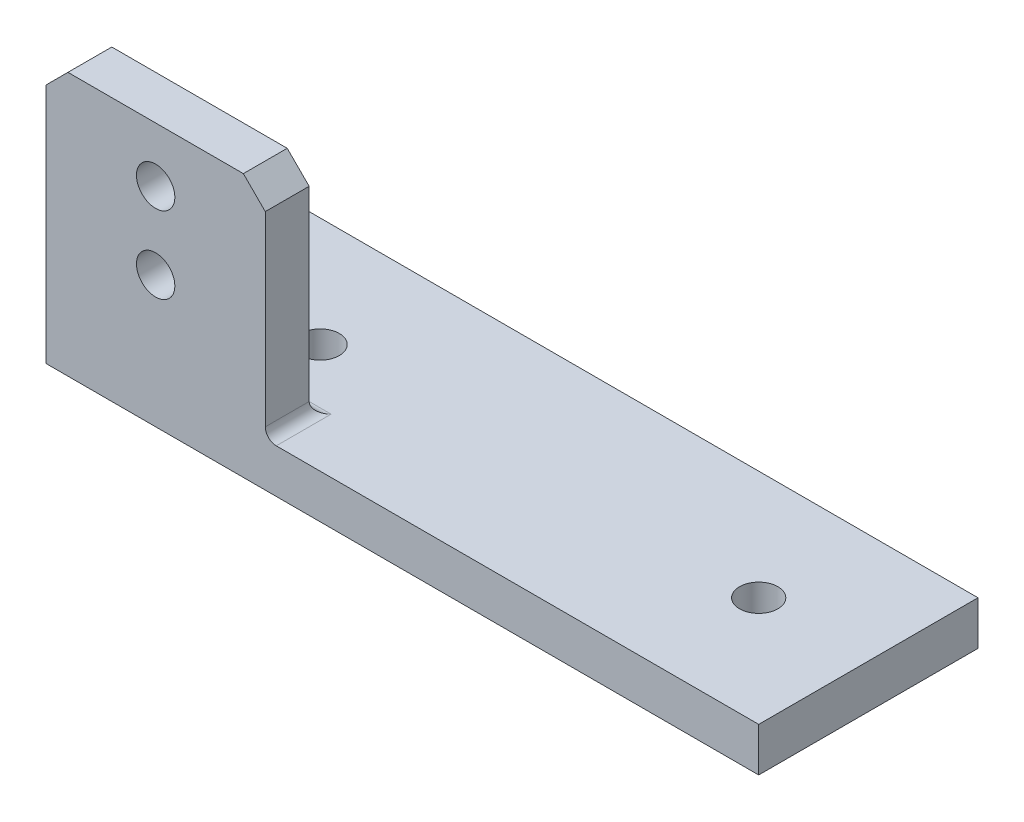
SolidWorks part; units mm, degrees
ref_plane "Piano frontale" through (0, 0, 0) normal (0, 0, 1) x (1, 0, 0)
ref_plane "Piano superiore" through (0, 0, 0) normal (0, 1, 0) x (1, 0, 0)
ref_plane "Piano destro" through (0, 0, 0) normal (1, 0, 0) x (0, 0, -1)
sketch "Schizzo1" plane through (0, 0, 0) normal (0, 0, 1) x (1, 0, 0)
  line L0 (0, 0) -> (65, 0)
  line L1 (65, 0) -> (65, 4)
  line L2 (65, 4) -> (0, 4)
  line L3 (0, 4) -> (0, 0)
  dimension "D1" = 4
  dimension "D2" = 65
extrude "Estrusione-Estrusione1" add sketch "Schizzo1" along normal blind 20
sketch "Schizzo2" plane through (0, 4, 0) normal (0, 1, 0) x (1, 0, 0)
  line L1 (0, -20) -> (20, -20)
  line L2 (0, -20) -> (0, -16)
  line L3 (0, -16) -> (20, -16)
  line L4 (20, -20) -> (20, -16)
  dimension "D1" = 4
  dimension "D2" = 20
extrude "Estrusione-Estrusione2" add sketch "Schizzo2" along normal blind 20
sketch "Schizzo6" plane through (0, 4, 0) normal (0, 1, 0) x (1, 0, 0)
  line L0 (65, -10) -> (0, -10) construction
  line L3 (65, -20) -> (65, 0) construction
  line L4 (0, -16) -> (0, 0) construction
  circle A0 centre (15, -10) radius 1.75
  circle A1 centre (55, -10) radius 1.75
  dimension "D1" = 3.5
  dimension "D2" = 10
  dimension "D3" = 40
extrude "Taglio-Estrusione1" cut sketch "Schizzo6" against normal up to next
sketch "Schizzo7" plane through (0, 0, 16) normal (0, 0, -1) x (-1, 0, 0)
  line L0 (-10, 24) -> (-10, 4) construction
  line L1 (-20, 24) -> (0, 24) construction
  line L2 (-20, 4) -> (0, 4) construction
  circle A0 centre (-10, 19) radius 1.75
  circle A1 centre (-10, 12) radius 1.75
  dimension "D1" = 3.5
  dimension "D2" = 5
  dimension "D3" = 7
extrude "Taglio-Estrusione2" cut sketch "Schizzo7" against normal up to next
fillet "Raccordo1" radius 1 1 edges
fillet "Raccordo2" radius 1 1 edges
chamfer "Smusso1" distance 2 angle 45 2 edges at (0, 24, 18) (20, 24, 18)
chamfer "Smusso3" distance 2 angle 45 1 edges at (0, 2, 0)
